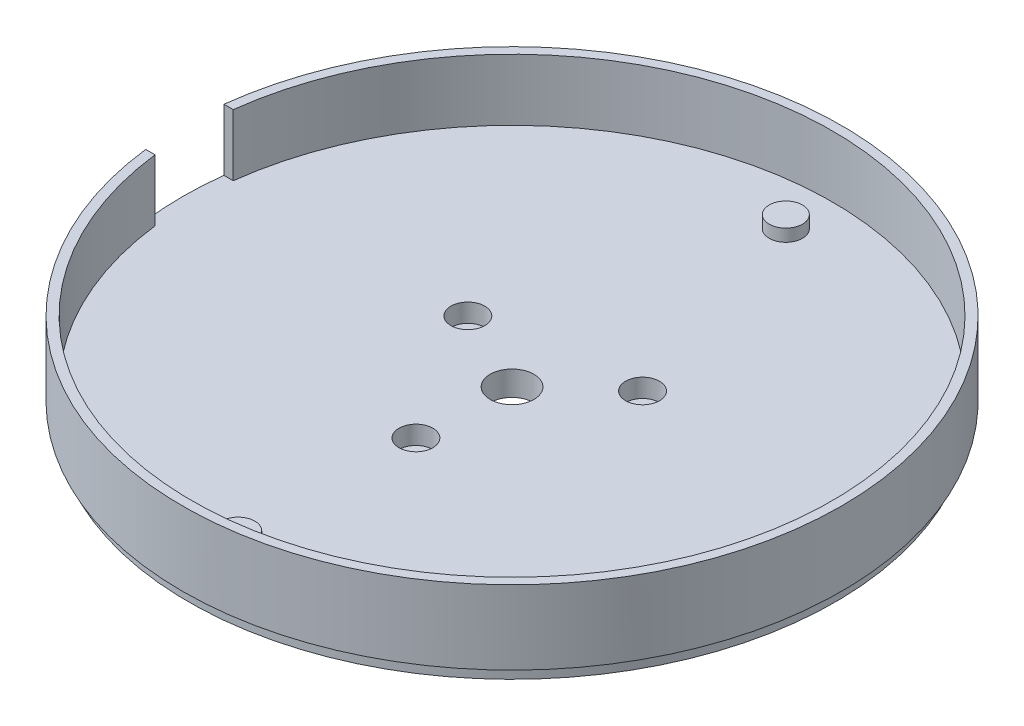
SolidWorks part; units mm, degrees
ref_plane "Front Plane" through (0, 0, 0) normal (0, 0, 1) x (1, 0, 0)
ref_plane "Top Plane" through (0, 0, 0) normal (0, 1, 0) x (1, 0, 0)
ref_plane "Right Plane" through (0, 0, 0) normal (1, 0, 0) x (0, 0, -1)
sketch "Sketch1" plane through (0, 0, 0) normal (0, 1, 0) x (1, 0, 0)
  circle A0 centre (0, 0) radius 53.5
  dimension "D1" = 107
extrude "Boss-Extrude1" add sketch "Sketch1" along normal blind 2
sketch "Sketch2" plane through (0, 2, 0) normal (0, 1, 0) x (1, 0, 0)
  circle A0 centre (0, -44.45) radius 2.7
  circle A1 centre (0, 44.45) radius 2.7
  dimension "D1" = 5.4
  dimension "D2" = 5.4
  dimension "D3" = 88.9
  dimension "D4" = 44.45
extrude "Boss-Extrude2" add sketch "Sketch2" along normal blind 2
sketch "Sketch3" plane through (0, 2, 0) normal (0, 1, 0) x (1, 0, 0)
  circle A0 centre (0, 0) radius 3.55
  dimension "D1" = 7.1
extrude "Cut-Extrude1" cut sketch "Sketch3" against normal blind 2 contours A0
sketch "Sketch7" plane through (0, 2, 0) normal (0, 1, 0) x (1, 0, 0)
  circle A0 centre (0, 0) radius 53.5
  circle A1 centre (0, 0) radius 52
  dimension "D1" = 107
  dimension "D2" = 104
extrude "Boss-Extrude3" add sketch "Sketch7" along normal blind 10
sketch "Sketch8" plane through (0, 2, 0) normal (0, 1, 0) x (1, 0, 0)
  line L0 (0, -6.35) -> (0, 6.35)
  line L1 (0, 6.35) -> (-56.6518, 6.35)
  line L3 (0, -6.35) -> (-56.6518, -6.35)
  line L4 (-56.6518, 6.35) -> (-56.6518, -6.35)
  line L5 (0, -6.35) -> (0, 6.35) construction
  line L6 (0, 0) -> (-56.6518, 0) construction
  point P0 (0, 0)
  dimension "D1" = 12.7
extrude "Cut-Extrude4" cut sketch "Sketch8" along normal up to surface (10 mm away) contours L4 L3 L0 L1 up to face at (0, 12, 53.5)
sketch "Sketch12" plane through (0, 2, 0) normal (0, 1, 0) x (1, 0, 0)
  circle A0 centre (11.169, 10.0127) radius 2.75
  circle A1 centre (-0.6161, -14.9873) radius 2.75
  circle A2 centre (-13.568, 6.396) radius 2.75
  circle A3 centre (0, 0) radius 3.55 construction
  dimension "D3" = 15
  dimension "D4" = 5.5
  dimension "D5" = 5.5
  dimension "D6" = 5.5
  dimension "D7" = 25
  dimension "D8" = 25
  dimension "D9" = 25
  dimension "D1" = 15
  dimension "D2" = 15
sketch "Sketch13" plane through (0, 0, 0) normal (0, -1, 0) x (1, 0, 0)
  circle A0 centre (0, 0) radius 52.5
  circle A1 centre (0, 0) radius 3.55
extrude "Boss-Extrude4" add sketch "Sketch13" along normal blind 2
extrude "Cut-Extrude6" cut sketch "Sketch12" against normal blind 3 contours A2 | A1 | A0
sketch "Sketch16" plane through (0, -1, 0) normal (0, 1, 0) x (1, 0, 0)
  circle A0 centre (11.169, 10.0127) radius 1.5
  circle A1 centre (-0.6161, -14.9873) radius 1.5
  circle A2 centre (-13.568, 6.396) radius 1.5
  dimension "D1" = 3
  dimension "D2" = 3
  dimension "D3" = 3
extrude "Cut-Extrude8" cut sketch "Sketch16" against normal through all contours A2 | A1 | A0
